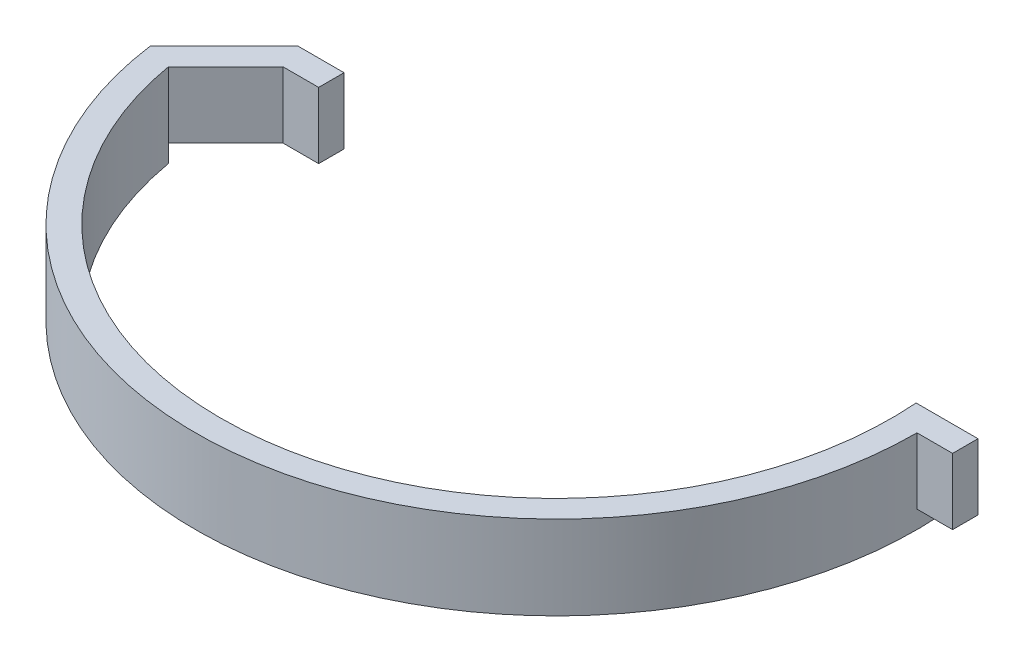
SolidWorks part; units mm, degrees
ref_plane "Front Plane" through (0, 0, 0) normal (0, 0, 1) x (1, 0, 0)
ref_plane "Top Plane" through (0, 0, 0) normal (0, 1, 0) x (1, 0, 0)
ref_plane "Right Plane" through (0, 0, 0) normal (1, 0, 0) x (0, 0, -1)
sketch "Sketch1" plane through (0, 0, 0) normal (0, 1, 0) x (1, 0, 0)
  line L0 (70.8103, 0) -> (65.8103, 0) construction
  line L3 (-65.8103, -10) -> (-70.3436, -14.5333) construction
  line L4 (-70.3436, -14.5333) -> (-55.8103, 0)
  line L5 (-55.8103, 0) -> (-46.7393, 0)
  line L6 (-46.7393, 0) -> (-46.7393, -5)
  line L7 (-46.7393, -5) -> (-53.7393, -5)
  line L8 (-53.7393, -5) -> (-65.0275, -16.2882)
  line L9 (65.8103, 0) -> (77.9866, 0)
  line L10 (77.9866, 0) -> (77.9866, -5)
  line L11 (77.9866, -5) -> (70.9866, -5)
  arc A0 (65.8103, 0) -> (-65.8103, -10) centre (0, -5) cw construction
  arc A2 (-70.3436, -14.5333) -> (70.8103, 0) centre (0, -5) ccw construction
  arc A4 (-65.0275, -16.2882) -> (65.8103, 0) centre (0, -5) ccw
  arc A5 (-70.3436, -14.5333) -> (70.9866, -5) centre (0, -5) ccw
  dimension "D2" = 66
  dimension "D1" = 5
  dimension "D3" = 5
  dimension "D4" = 45
  dimension "D5" = 10
  dimension "D6" = 7
  dimension "D7" = 5
extrude "Boss-Extrude1" add sketch "Sketch1" along normal blind 13
sketch "Sketch2" plane through (0, 0, 0) normal (0, -1, 0) x (1, 0, 0)
  line L0 (-65.0275, 16.2882) -> (-68.563, 12.7527)
  line L1 (-55.8103, 0) -> (-70.3436, 14.5333) construction
  line L2 (-68.563, 12.7527) -> (-70.3436, 14.5333)
  line L3 (65.8103, 0) -> (70.8103, 0)
  line L4 (77.9866, 0) -> (65.8103, 0) construction
  arc A0 (65.8103, 0) -> (-65.0275, 16.2882) centre (0, 5) ccw construction
  arc A1 (65.8103, 0) -> (-65.0275, 16.2882) centre (0, 5) ccw
  arc A2 (-70.3436, 14.5333) -> (70.8103, 0) centre (0, 5) cw
extrude "Boss-Extrude2" add sketch "Sketch2" along normal blind 3.5
